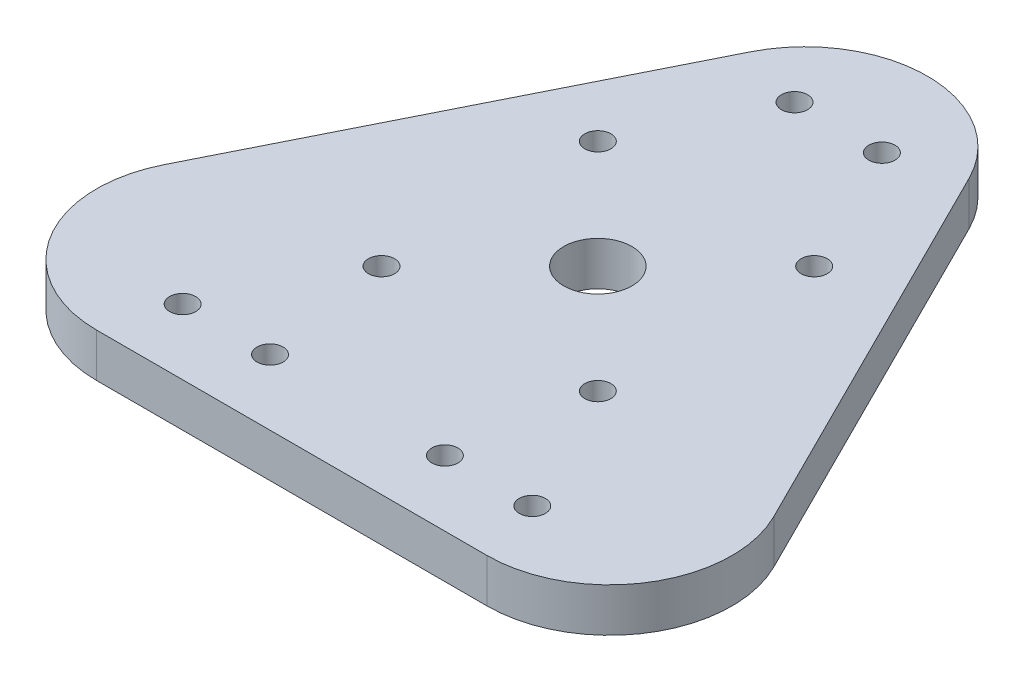
SolidWorks part; units mm, degrees
material "6061-T6 (SS)"
ref_plane "Front Plane" through (0, 0, 0) normal (0, 0, 1) x (1, 0, 0)
ref_plane "Top Plane" through (0, 0, 0) normal (0, 1, 0) x (1, 0, 0)
ref_plane "Right Plane" through (0, 0, 0) normal (1, 0, 0) x (0, 0, -1)
sketch "Sketch1" plane through (0, 0, 0) normal (0, 1, 0) x (1, 0, 0)
  line L0 (-57.15, 0) -> (0, 114.3)
  line L1 (0, 114.3) -> (57.15, 0)
  line L2 (0, 114.3) -> (0, 0) construction
  line L3 (-57.15, 0) -> (57.15, 0)
  line L4 (-31.75, 3.175) -> (-31.75, 15.875) construction
  line L5 (6.35, 3.175) -> (31.75, 3.175) construction
  line L6 (6.35, 3.175) -> (6.35, 15.875) construction
  line L7 (6.35, 15.875) -> (31.75, 15.875) construction
  line L8 (31.75, 3.175) -> (31.75, 15.875) construction
  line L9 (-12.7, 73.025) -> (12.7, 73.025) construction
  line L10 (-12.7, 73.025) -> (-12.7, 85.725) construction
  line L11 (-12.7, 85.725) -> (12.7, 85.725) construction
  line L12 (12.7, 73.025) -> (12.7, 85.725) construction
  line L13 (-6.35, 15.875) -> (-31.75, 15.875) construction
  line L14 (-6.35, 3.175) -> (-6.35, 15.875) construction
  line L15 (-6.35, 3.175) -> (-31.75, 3.175) construction
  point P0 (0, 0)
  dimension "D3" = 12.7
  dimension "D1" = 114.3
  dimension "D2" = 114.3
  dimension "D4" = 25.4
  dimension "D5" = 57.15
  dimension "D6" = 3.175
  dimension "D7" = 12.7
extrude "Boss-Extrude1" add sketch "Sketch1" against normal blind 6.35
hole_wizard "#6 Clearance Hole1" positions "Sketch3" profile "Sketch2" hole size "#6" standard "ANSI Inch" end condition through all
sketch "Sketch3" plane through (0, 0, 0) normal (0, 1, 0) x (1, 0, 0)
  line L0 (-12.7, 85.725) -> (12.7, 85.725) construction
  line L1 (-12.7, 73.025) -> (-12.7, 85.725) construction
  line L2 (-12.7, 73.025) -> (12.7, 73.025) construction
  line L3 (12.7, 73.025) -> (12.7, 85.725) construction
  line L4 (6.35, 15.875) -> (31.75, 15.875) construction
  line L5 (6.35, 3.175) -> (6.35, 15.875) construction
  line L6 (6.35, 3.175) -> (31.75, 3.175) construction
  line L7 (31.75, 3.175) -> (31.75, 15.875) construction
  line L8 (-12.7, 85.725) -> (12.7, 85.725) construction
  line L9 (-12.7, 73.025) -> (-12.7, 85.725) construction
  line L10 (-12.7, 73.025) -> (12.7, 73.025) construction
  line L11 (12.7, 73.025) -> (12.7, 85.725) construction
  line L12 (6.35, 15.875) -> (31.75, 15.875) construction
  line L13 (6.35, 3.175) -> (6.35, 15.875) construction
  line L14 (6.35, 3.175) -> (31.75, 3.175) construction
  line L15 (31.75, 3.175) -> (31.75, 15.875) construction
  line L16 (0, 0) -> (0, 114.3) construction
  line L17 (-57.15, 0) -> (57.15, 0) construction
  line L20 (19.05, 15.875) -> (19.05, 3.175) construction
  line L21 (12.7, 9.525) -> (25.4, 9.525) construction
  line L23 (-6.35, 79.375) -> (6.35, 79.375) construction
  point P32 (25.4, 9.525)
  point P34 (12.7, 9.525)
  point P37 (-6.35, 79.375)
  point P39 (6.35, 79.375)
  point P53 (-25.4, 9.525)
  point P54 (-12.7, 9.525)
  dimension "D1" = 12.7
sketch "Sketch2" plane through (25.4, 0, -9.525) normal (1, 0, 0) x (0, 0, 1)
  line L0 (0, 0) -> (0, 6.35)
  line L1 (0, 6.35) -> (1.8986, 6.35)
  line L2 (1.8986, 6.35) -> (1.8986, 0)
  line L5 (1.8986, 0) -> (0, 0)
  line L11 (0, -6.35) -> (0, 107.95) construction
  dimension "Thru Hole Dia." = 3.7973
  dimension "Thru Hole Depth" = 6.35
fillet "Fillet1" radius 17.78 3 edges at (0, -3.175, -114.3) (57.15, -3.175, 0) (-57.15, -3.175, 0)
hole_wizard "7/16-20 Tapped Hole1" positions "Sketch6" profile "Sketch5" tap size "7/16-20" standard "ANSI Inch" end condition through all
sketch "Sketch6" plane through (0, 0, 0) normal (0, 1, 0) x (1, 0, 0)
  circle A0 centre (-12.7, 9.525) radius 1.8986 construction
  point P0 (0, 44.45)
  dimension "D1" = 34.925
sketch "Sketch5" plane through (0, 0, -44.45) normal (1, 0, 0) x (0, 0, 1)
  line L0 (0, 0) -> (0, 6.35)
  line L1 (0, 6.35) -> (4.9606, 6.35)
  line L2 (4.9606, 6.35) -> (4.9606, 0)
  line L5 (4.9606, 0) -> (0, 0)
  line L11 (0, -6.35) -> (0, 107.95) construction
  dimension "Thread Major Dia." = 9.9212
  dimension "Thru Tap Drill Depth" = 6.35
hole_wizard "#6 Clearance Hole2" positions "Sketch8" profile "Sketch7" hole size "#6" standard "ANSI Inch" end condition up to next
sketch "Sketch8" plane through (0, 0, 0) normal (0, 1, 0) x (1, 0, 0)
  line L0 (15.7154, 60.1654) -> (0, 44.45) construction
  line L2 (-15.7154, 60.1654) -> (0, 44.45) construction
  line L4 (0, 44.45) -> (0, 76.1788) construction
  circle A0 centre (0, 44.45) radius 22.225
  point P5 (-15.7154, 60.1654)
  point P7 (15.7154, 28.7346)
  point P9 (-15.7154, 28.7346)
  point P11 (15.7154, 60.1654)
  dimension "D1" = 44.45
  dimension "D2" = 90
  dimension "D3" = 45
sketch "Sketch7" plane through (-15.7154, 0, -60.1654) normal (1, 0, 0) x (0, 0, 1)
  line L0 (0, 0) -> (0, 6.35)
  line L1 (0, 6.35) -> (1.8986, 6.35)
  line L2 (1.8986, 6.35) -> (1.8986, 0)
  line L5 (1.8986, 0) -> (0, 0)
  line L11 (0, -6.35) -> (0, 107.95) construction
  dimension "Thru Hole Dia." = 3.7973
  dimension "Thru Hole Depth" = 6.35
